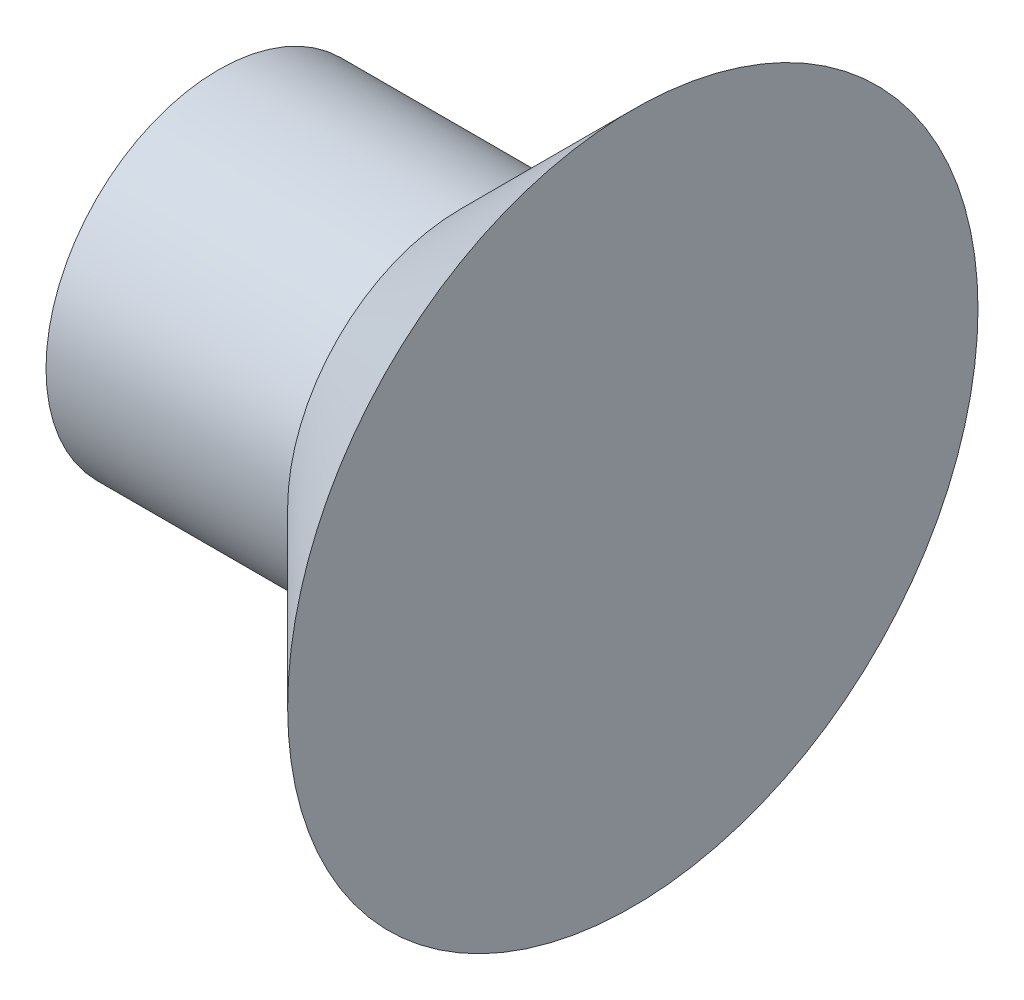
SolidWorks part; units mm, degrees
ref_plane "Plan de face" through (0, 0, 0) normal (0, 0, 1) x (1, 0, 0)
ref_plane "Plan de dessus" through (0, 0, 0) normal (0, 1, 0) x (1, 0, 0)
ref_plane "Plan de droite" through (0, 0, 0) normal (1, 0, 0) x (0, 0, -1)
sketch "Esquisse1" plane through (0, 0, 0) normal (0, 0, 1) x (1, 0, 0)
  line L0 (0, 0) -> (-3, 0)
  line L1 (-3, 0) -> (-3, 1.25)
  line L2 (-3, 1.25) -> (-1.25, 1.25)
  line L3 (-1.25, 1.25) -> (0, 2.5)
  line L4 (0, 2.5) -> (0, 0)
  line L5 (0, 0) -> (21.1509, 0) construction
  dimension "D1" = 45
  dimension "D2" = 1.25
  dimension "D3" = 2.5
  dimension "D4" = 3
revolve "Révolution1" add sketch "Esquisse1" angle 360 about L5
